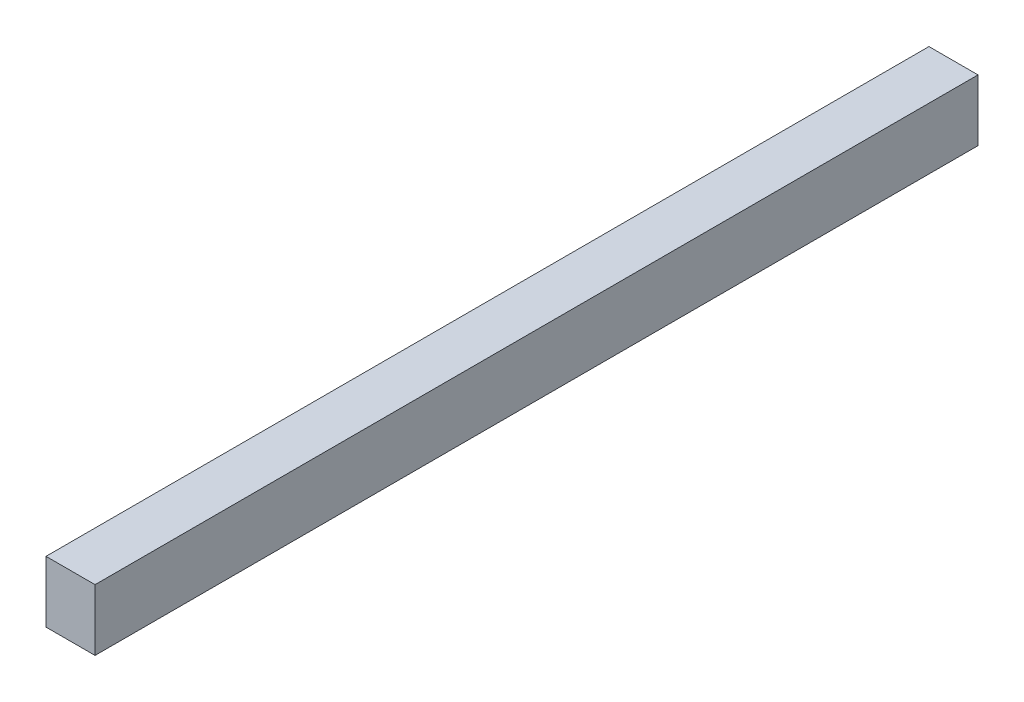
SolidWorks part; units mm, degrees
ref_plane "Front Plane" through (0, 0, 0) normal (0, 0, 1) x (1, 0, 0)
ref_plane "Top Plane" through (0, 0, 0) normal (0, 1, 0) x (1, 0, 0)
ref_plane "Right Plane" through (0, 0, 0) normal (1, 0, 0) x (0, 0, -1)
sketch "Sketch1" plane through (0, 0, 0) normal (0, 0, 1) x (1, 0, 0)
  line L1 (-12.7, -15.875) -> (12.7, -15.875)
  line L2 (-12.7, -15.875) -> (-12.7, 15.875)
  line L3 (-12.7, 15.875) -> (12.7, 15.875)
  line L4 (12.7, -15.875) -> (12.7, 15.875)
  line L5 (-12.7, -15.875) -> (12.7, 15.875) construction
  line L6 (-12.7, 15.875) -> (12.7, -15.875) construction
  point P0 (0, 0)
  dimension "D1" = 25.4
  dimension "D2" = 31.75
extrude "Boss-Extrude1" add sketch "Sketch1" along normal blind 457.2
